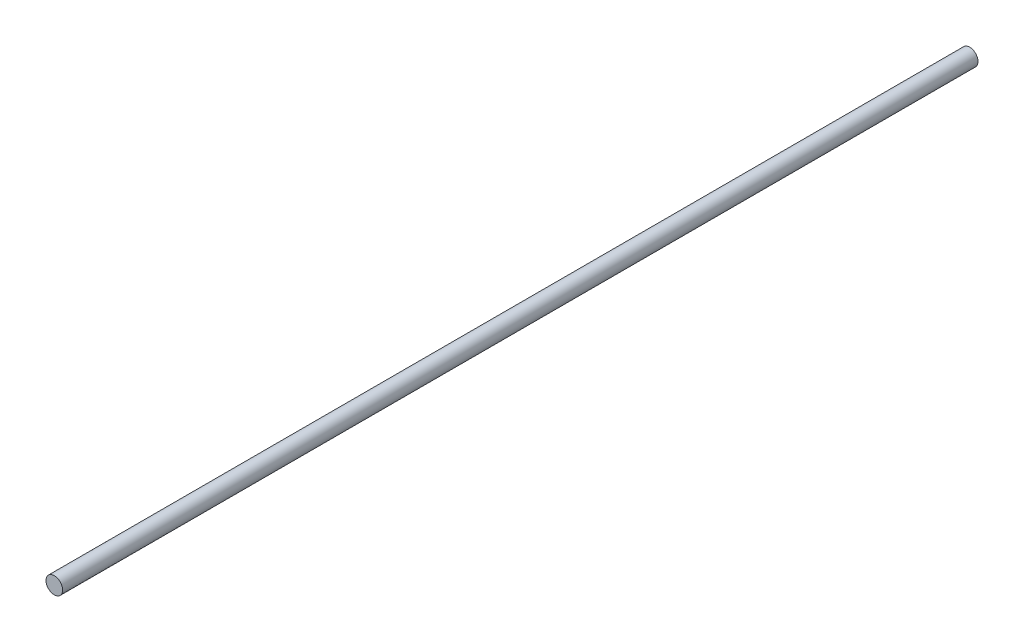
SolidWorks part; units mm, degrees
ref_plane "Front Plane" through (0, 0, 0) normal (0, 0, 1) x (1, 0, 0)
ref_plane "Top Plane" through (0, 0, 0) normal (0, 1, 0) x (1, 0, 0)
ref_plane "Right Plane" through (0, 0, 0) normal (1, 0, 0) x (0, 0, -1)
sketch "Sketch1" plane through (0, 0, 0) normal (0, 0, 1) x (1, 0, 0)
  circle A0 centre (0, 0) radius 3.175
  dimension "D1" = 6.35
extrude "Boss-Extrude1" add sketch "Sketch1" along normal blind 349.426
sketch "Sketch2" plane through (0, 0, 349.426) normal (0, 0, 1) x (1, 0, 0)
  circle A0 centre (0, 0) radius 3.175
  circle A1 centre (0, 0) radius 3.175 construction
